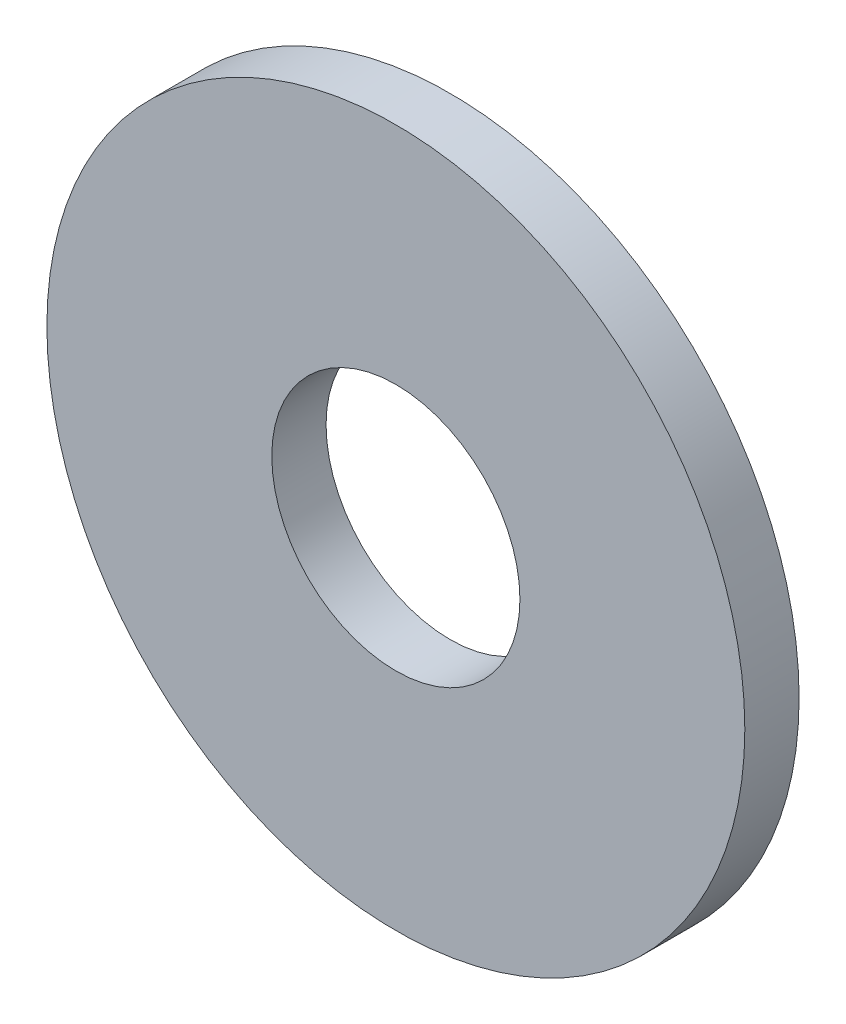
SolidWorks part; units mm, degrees
ref_plane "Front Plane" through (0, 0, 0) normal (0, 0, 1) x (1, 0, 0)
ref_plane "Top Plane" through (0, 0, 0) normal (0, 1, 0) x (1, 0, 0)
ref_plane "Right Plane" through (0, 0, 0) normal (1, 0, 0) x (0, 0, -1)
sketch "Sketch1" plane through (0, 0, 0) normal (0, 0, 1) x (1, 0, 0)
  circle A0 centre (0, 0) radius 1.6
  circle A1 centre (0, 0) radius 4.5
  dimension "ID" = 3.2
  dimension "OD" = 9
extrude "Extrude1" add sketch "Sketch1" against normal blind 0.7
